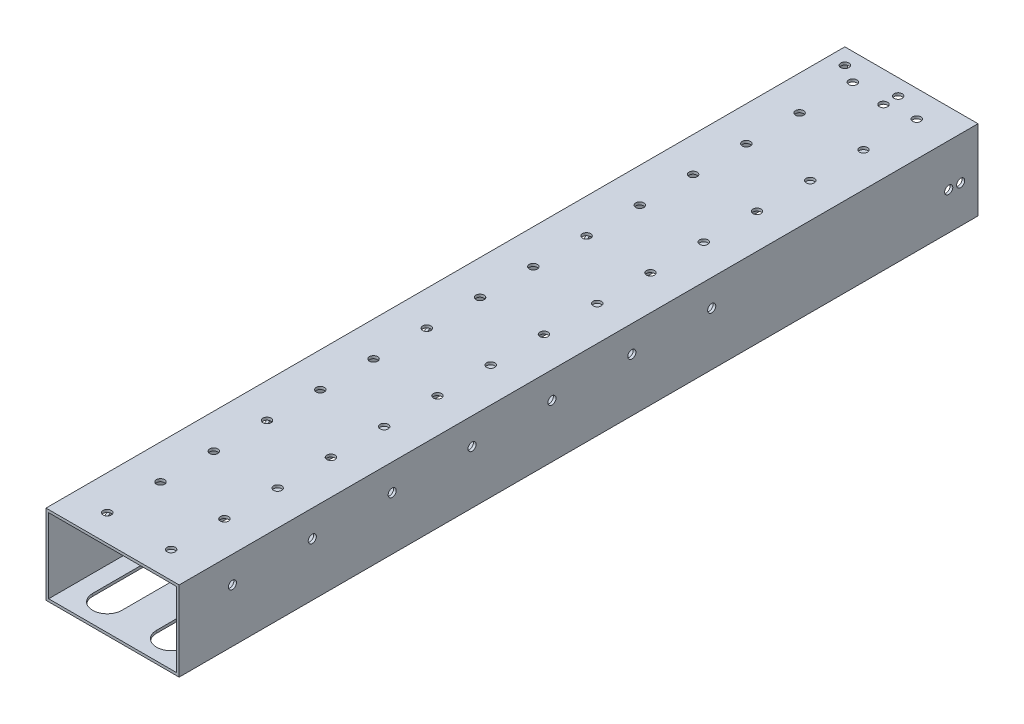
SolidWorks part; units mm, degrees
material "6063-T5"
ref_plane "前视基准面" through (0, 0, 0) normal (0, 0, 1) x (1, 0, 0)
ref_plane "上视基准面" through (0, 0, 0) normal (0, 1, 0) x (1, 0, 0)
ref_plane "右视基准面" through (0, 0, 0) normal (1, 0, 0) x (0, 0, -1)
sketch "草图2" plane through (0, 0, 0) normal (0, 0, 1) x (1, 0, 0)
  line L0 (-24, -14) -> (-24, 14)
  line L1 (-25, -15) -> (25, -15)
  line L2 (-25, -15) -> (-25, 15)
  line L3 (-25, 15) -> (25, 15)
  line L4 (25, -15) -> (25, 15)
  line L5 (0, 15) -> (0, -15) construction
  line L6 (-25, 0) -> (25, 0) construction
  line L7 (-24, 14) -> (24, 14)
  line L8 (24, -14) -> (24, 14)
  line L9 (-24, -14) -> (24, -14)
  point P0 (0, 0)
  dimension "D1" = 50
  dimension "D2" = 30
  dimension "D3" = 1
extrude "凸台-拉伸1" add sketch "草图2" along normal mid plane 300
sketch "草图3" plane through (25, 0, 0) normal (1, 0, 0) x (0, 0, -1)
  circle A0 centre (-130, 5) radius 1.525 construction
  circle A1 centre (-130, 5) radius 1.525
extrude "切除-拉伸1" cut sketch "草图3" against normal blind 10
pattern_linear "阵列(线性)1" count 7 spacing 30 along (0, 0, -1) of "切除-拉伸1"
sketch "草图4" plane through (0, 15, 0) normal (0, 1, 0) x (1, 0, 0)
  circle A0 centre (12, 140) radius 1.75 construction
  circle A1 centre (-12, 140) radius 1.75 construction
  circle A2 centre (12, 140) radius 1.75 construction
  circle A3 centre (-12, 140) radius 1.75 construction
  circle A4 centre (-12, 140) radius 1.525
  circle A5 centre (12, 140) radius 1.525
  dimension "D1" = 3.05
extrude "切除-拉伸2" cut sketch "草图4" against normal blind 10
pattern_linear "阵列(线性)2" count 15 spacing 20 along (0, 0, 1) of "切除-拉伸2"
sketch "草图5" plane through (0, -14, 0) normal (0, 1, 0) x (1, 0, 0)
  line L0 (-12, -140) -> (-12, -120) construction
  line L1 (-17.5, -140) -> (-17.5, -120)
  line L2 (-6.5, -140) -> (-6.5, -120)
  line L3 (0, 0) -> (0, -162.0559) construction
  line L4 (12, -140) -> (12, -120) construction
  line L5 (17.5, -140) -> (17.5, -120)
  line L6 (6.5, -140) -> (6.5, -120)
  arc A0 (-17.5, -140) -> (-6.5, -140) centre (-12, -140) ccw
  arc A1 (-6.5, -120) -> (-17.5, -120) centre (-12, -120) ccw
  arc A2 (17.5, -140) -> (6.5, -140) centre (12, -140) cw
  arc A3 (6.5, -120) -> (17.5, -120) centre (12, -120) cw
  point P4 (-12, -130)
  point P14 (12, -130)
  dimension "D1" = 5.5
extrude "切除-拉伸3" cut sketch "草图5" against normal blind 10
pattern_linear "阵列(线性)3" count 7 spacing 40 along (0, 0, -1) of "切除-拉伸3"
sketch "草图6" plane through (-24, 0, 0) normal (1, 0, 0) x (0, 0, -1)
  circle A0 centre (-130, 5) radius 4
  dimension "D1" = 8
extrude "切除-拉伸4" cut sketch "草图6" against normal blind 10
pattern_linear "阵列(线性)4" count 7 spacing 30 along (0, 0, -1) of "切除-拉伸4"
sketch "草图7" plane through (0, -15, 0) normal (0, -1, 0) x (1, 0, 0)
  circle A0 centre (-19, -144) radius 1.25 construction
  circle A1 centre (1, -144) radius 1.25 construction
  circle A2 centre (-19, -144) radius 1.25 construction
  circle A3 centre (1, -144) radius 1.25 construction
  circle A4 centre (-19, -144) radius 1.525
  circle A5 centre (1, -144) radius 1.525
  dimension "D1" = 3.05
extrude "切除-拉伸5" cut sketch "草图7" against normal blind 90
sketch "草图8" plane through (0, -15, 0) normal (0, -1, 0) x (1, 0, 0)
  line L0 (12, 0) -> (12, -20) construction
  line L1 (-19, -90) -> (19, -90) construction
  line L2 (-19, -90) -> (-19, 70) construction
  line L3 (-19, 70) -> (19, 70) construction
  line L4 (19, -90) -> (19, 70) construction
  line L5 (0, 70) -> (0, -90) construction
  line L6 (-19, -10) -> (19, -10) construction
  line L7 (12, -10) -> (19, -10) construction
  line L8 (25, 150) -> (25, -150) construction
  line L9 (12, -80) -> (12, -100) construction
  line L10 (19, -90) -> (12, -90) construction
  circle A0 centre (19, -10) radius 1.525
  circle A1 centre (-19, -10) radius 1.525
  circle A2 centre (-19, -90) radius 1.525
  circle A3 centre (19, -90) radius 1.525
  circle A4 centre (-19, 70) radius 1.525
  circle A5 centre (19, 70) radius 1.525
  point P0 (0, -10)
  dimension "D2" = 3.05
  dimension "D1" = 6
extrude "切除-拉伸6" cut sketch "草图8" against normal blind 10
sketch "草图10" plane through (25, 0, 0) normal (1, 0, 0) x (0, 0, -1)
  line L0 (150, -15) -> (150, 15) construction
  circle A0 centre (139, -1) radius 1.525
  dimension "D1" = 3.05
  dimension "D2" = 11
  dimension "D3" = 1
extrude "切除-拉伸7" cut sketch "草图10" against normal through all
sketch "草图11" plane through (0, -15, 0) normal (0, -1, 0) x (1, 0, 0)
  line L0 (1, -150) -> (1, -144) construction
  line L1 (-25, -150) -> (25, -150) construction
  circle A0 centre (-6, -144) radius 1.525
  circle A2 centre (1, -144) radius 1.525 construction
  dimension "D1" = 3.05
  dimension "D2" = 7
sketch "草图12" plane through (0, -15, 0) normal (0, -1, 0) x (1, 0, 0)
  line L0 (1, -144) -> (1, -138.5) construction
  circle A0 centre (1, -138.5) radius 1.525
  circle A1 centre (1, -144) radius 1.525 construction
  dimension "D2" = 3.05
  dimension "D1" = 5.5
extrude "切除-拉伸9" cut sketch "草图12" against normal through all both and the other way through all
sketch "草图14" plane through (25, 0, 0) normal (1, 0, 0) x (0, 0, -1)
  line L0 (150, -15) -> (150, 15) construction
  line L1 (139, -1) -> (143.5, -1) construction
  circle A0 centre (143.5, -1) radius 1.525
  dimension "D1" = 6.5
  dimension "D2" = 3.05
extrude "切除-拉伸10" cut sketch "草图14" against normal blind 10
